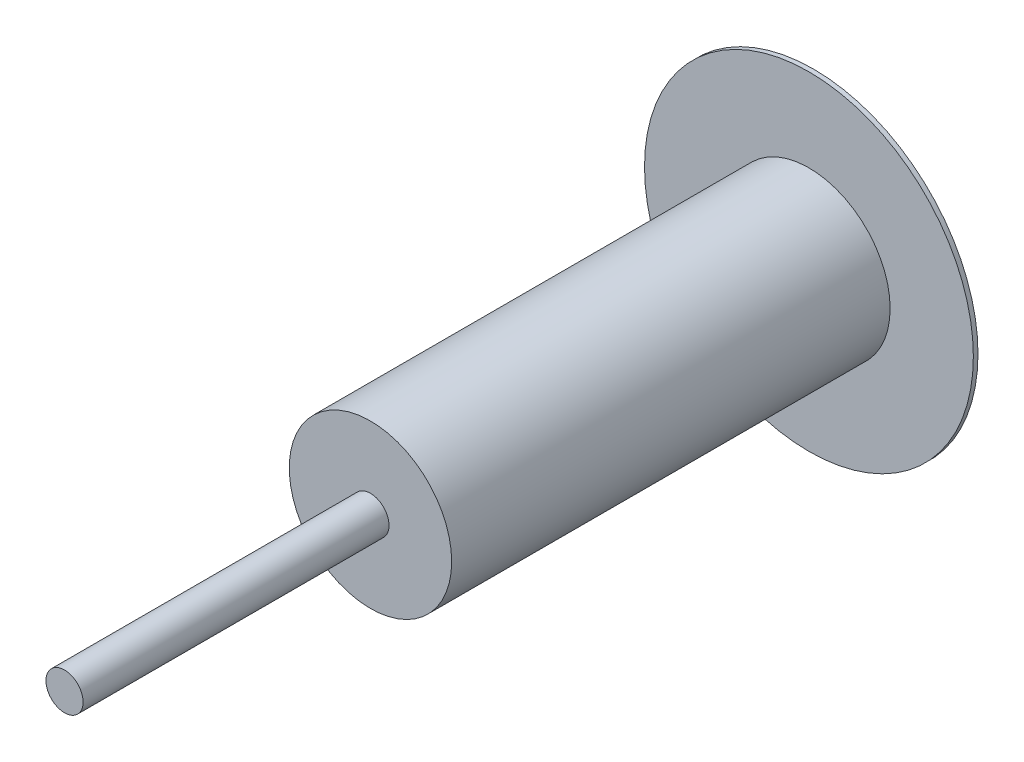
SolidWorks part; units mm, degrees
other "Markup1"
sketch "Sketch6" plane through (500, -500, -1363.6) normal (1, 0, 0) x (0, 0, -1)
ref_plane "Top Plane" through (0, 0, 0) normal (0, 0, 1) x (1, 0, 0)
ref_plane "Right Plane" through (0, 0, 0) normal (0, 1, 0) x (1, 0, 0)
ref_plane "Front Plane" through (0, 0, 0) normal (1, 0, 0) x (0, 0, -1)
sketch "Sketch1" plane through (0, 0, 0) normal (0, 0, 1) x (1, 0, 0)
  circle A0 centre (0, 0) radius 50.8
  dimension "D1" = 101.6
extrude "Boss-Extrude1" add sketch "Sketch1" against normal blind 1363.6 and the other way blind 686.4
sketch "Sketch2" plane through (0, 0, -1363.6) normal (0, 0, 1) x (1, 0, 0)
  circle A0 centre (0, 0) radius 450
  dimension "D1" = 900
extrude "Boss-Extrude2" add sketch "Sketch2" along normal blind 12.7
sketch "Sketch3" plane through (0, 0, -1350.9) normal (0, 0, 1) x (1, 0, 0)
  circle A0 centre (0, 0) radius 222.25
  dimension "D1" = 444.5
extrude "Boss-Extrude3" add sketch "Sketch3" along normal blind 1200
